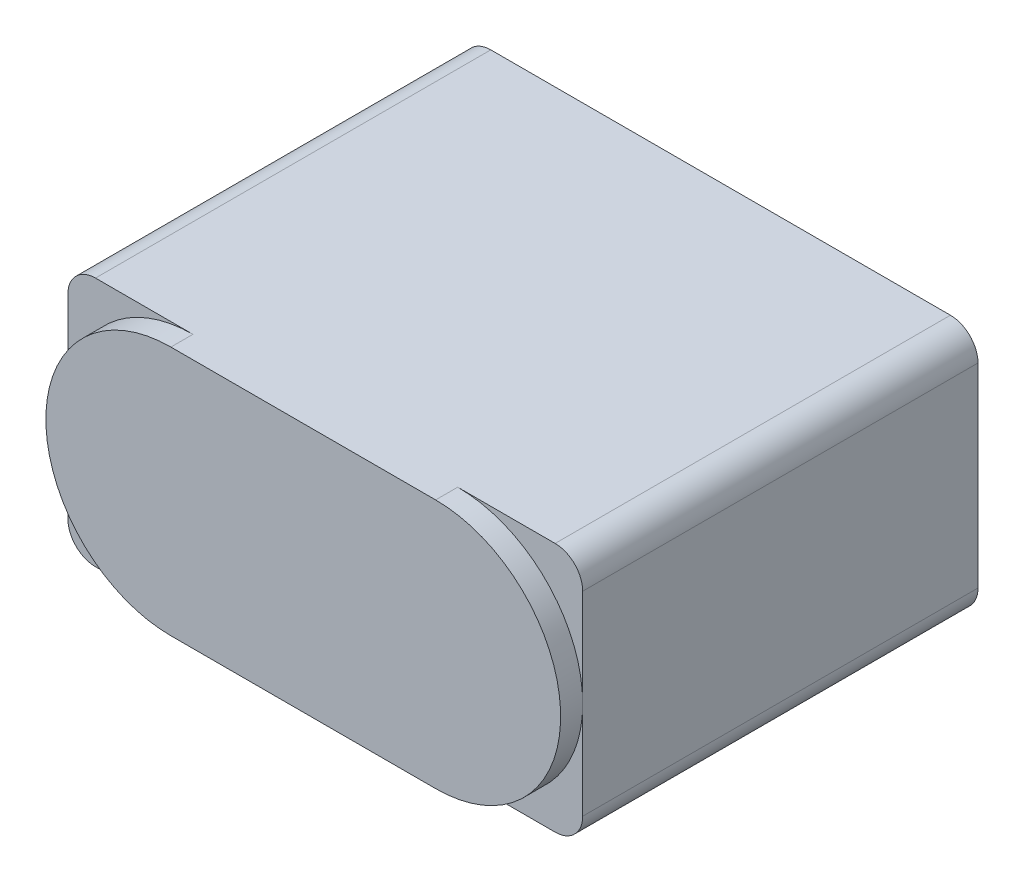
SolidWorks part; units mm, degrees
material "ABS"
ref_plane "前视基准面" through (0, 0, 0) normal (0, 0, 1) x (1, 0, 0)
ref_plane "上视基准面" through (0, 0, 0) normal (0, 1, 0) x (1, 0, 0)
ref_plane "右视基准面" through (0, 0, 0) normal (1, 0, 0) x (0, 0, -1)
sketch "草图1" plane through (0, 0, 0) normal (0, 0, 1) x (1, 0, 0)
  line L1 (1.5, 0) -> (26.5, 0)
  line L2 (0, 1.5) -> (0, 12.1)
  line L3 (1.5, 13.6) -> (26.5, 13.6)
  line L4 (28, 1.5) -> (28, 12.1)
  arc A0 (26.5, 0) -> (28, 1.5) centre (26.5, 1.5) ccw
  arc A1 (0, 12.1) -> (1.5, 13.6) centre (1.5, 12.1) cw
  arc A2 (26.5, 13.6) -> (28, 12.1) centre (26.5, 12.1) cw
  arc A3 (1.5, 0) -> (0, 1.5) centre (1.5, 1.5) cw
  point P7 (28, 0)
  point P10 (0, 13.6)
  point P15 (0, 0)
  dimension "D3" = 1.5
  dimension "D1" = 13.6
  dimension "D2" = 28
extrude "凸台-拉伸1" add sketch "草图1" along normal blind 22.7
sketch "草图2" plane through (0, 0, 22.7) normal (0, 0, 1) x (1, 0, 0)
  line L0 (6.8, 6.8) -> (21.2, 6.8) construction
  line L1 (6.8, 13.6) -> (21.2, 13.6)
  line L2 (6.8, 0) -> (21.2, 0)
  line L3 (14, 13.6) -> (14, -9.8871) construction
  line L4 (26.5, 13.6) -> (1.5, 13.6) construction
  line L5 (28, 6.8) -> (-1.3995, 6.8) construction
  line L6 (28, 1.5) -> (28, 12.1) construction
  line L7 (0, 12.1) -> (0, 1.5) construction
  line L12 (28, 1.5) -> (28, 12.1)
  line L13 (26.5, 13.6) -> (1.5, 13.6)
  line L14 (0, 12.1) -> (0, 1.5)
  line L15 (1.5, 0) -> (26.5, 0)
  line L16 (28, 1.5) -> (28, 12.1)
  line L17 (26.5, 13.6) -> (1.5, 13.6)
  line L18 (0, 12.1) -> (0, 1.5)
  line L19 (1.5, 0) -> (26.5, 0)
  arc A0 (6.8, 13.6) -> (6.8, 0) centre (6.8, 6.8) ccw
  arc A1 (21.2, 0) -> (21.2, 13.6) centre (21.2, 6.8) ccw
  arc A6 (26.5, 0) -> (28, 1.5) centre (26.5, 1.5) ccw
  arc A7 (28, 12.1) -> (26.5, 13.6) centre (26.5, 12.1) ccw
  arc A8 (1.5, 13.6) -> (0, 12.1) centre (1.5, 12.1) ccw
  arc A9 (0, 1.5) -> (1.5, 0) centre (1.5, 1.5) ccw
  arc A10 (26.5, 0) -> (28, 1.5) centre (26.5, 1.5) ccw
  arc A11 (28, 12.1) -> (26.5, 13.6) centre (26.5, 12.1) ccw
  arc A12 (1.5, 13.6) -> (0, 12.1) centre (1.5, 12.1) ccw
  arc A13 (0, 1.5) -> (1.5, 0) centre (1.5, 1.5) ccw
  point P2 (14, 6.8)
  arc M16 (26.5, 0) -> (28, 1.5) centre (26.5, 1.5) ccw
  line M17 (28, 1.5) -> (28, 12.1)
  arc M18 (28, 12.1) -> (26.5, 13.6) centre (26.5, 12.1) ccw
  line M19 (26.5, 13.6) -> (1.5, 13.6)
  arc M20 (1.5, 13.6) -> (0, 12.1) centre (1.5, 12.1) ccw
  line M21 (0, 12.1) -> (0, 1.5)
  arc M22 (0, 1.5) -> (1.5, 0) centre (1.5, 1.5) ccw
  line M23 (1.5, 0) -> (26.5, 0)
  dimension "D1" = 6.8
  dimension "D2" = 0
extrude "切除-拉伸1" cut sketch "草图2" against normal blind 1.2 contours A0 M19 M20 M21 | A0 L18 M22 M23 | A1 M23 M16 M17 | A1 L16 M18 M19
sketch "草图3" plane through (0, 0, 0) normal (0, 0, -1) x (-1, 0, 0)
  line L0 (-28, 6.8) -> (9.6728, 6.8) construction
  line L1 (-28, 1.5) -> (-28, 12.1) construction
  line L2 (-14, 13.6) -> (-14, -8.4705) construction
  line L3 (-26.5, 13.6) -> (-1.5, 13.6) construction
  line L5 (-18, 9.8) -> (-10, 9.8)
  line L6 (-18, 9.8) -> (-18, 3.8)
  line L7 (-18, 3.8) -> (-10, 3.8)
  line L8 (-10, 9.8) -> (-10, 3.8)
  circle A0 centre (-24.8, 6.8) radius 1.25
  circle A1 centre (-3.2, 6.8) radius 1.25
  dimension "D1" = 2.5
  dimension "D2" = 21.6
  dimension "D3" = 6
  dimension "D4" = 8
extrude "切除-拉伸2" cut sketch "草图3" against normal blind 5
cosmetic thread "装饰螺纹线3" parameters "D2"=3
cosmetic thread "装饰螺纹线4" parameters "D2"=3
sketch "草图4" plane through (0, 0, 0) normal (0, -1, 0) x (1, 0, 0)
  line L0 (6.8, 22.7) -> (21.2, 22.7) construction
  line L1 (14, 0) -> (14, 33.693) construction
  line L2 (1.5, 0) -> (26.5, 0) construction
  circle A0 centre (24.8, 11.6) radius 0.75
  circle A1 centre (3.2, 11.6) radius 0.75
  dimension "D3" = 1.5
  dimension "D1" = 11.1
  dimension "D2" = 21.6
extrude "切除-拉伸3" cut sketch "草图4" against normal blind 5
cosmetic thread "装饰螺纹线1" parameters "D2"=2
cosmetic thread "装饰螺纹线2" parameters "D2"=2
ref_plane "基准面1" through (0, 0, 262.7) normal (0, 0, 1) x (1, 0, 0)
sketch "草图5" plane through (0, 0, 262.7) normal (0, 0, 1) x (1, 0, 0)
  line L2 (21.2, 34.6) -> (6.8, 34.6)
  line L3 (6.8, -21) -> (21.2, -21)
  line L8 (6.8, 0) -> (21.2, 0)
  line L9 (21.2, 13.6) -> (6.8, 13.6)
  line L10 (6.8, 0) -> (21.2, 0) construction
  line L11 (21.2, 13.6) -> (6.8, 13.6) construction
  arc A2 (21.2, -21) -> (21.2, 34.6) centre (21.2, 6.8) ccw
  arc A3 (6.8, 34.6) -> (6.8, -21) centre (6.8, 6.8) ccw
  arc A8 (6.8, 13.6) -> (6.8, 0) centre (6.8, 6.8) ccw
  arc A9 (21.2, 0) -> (21.2, 13.6) centre (21.2, 6.8) ccw
  arc A10 (6.8, 13.6) -> (6.8, 0) centre (6.8, 6.8) ccw construction
  arc A11 (21.2, 0) -> (21.2, 13.6) centre (21.2, 6.8) ccw construction
  dimension "D3" = 0
  dimension "D1" = 21
sketch "草图6" plane through (0, 0, 22.7) normal (0, 0, 1) x (1, 0, 0)
  line L2 (6.8, 0) -> (21.2, 0)
  line L3 (21.2, 13.6) -> (6.8, 13.6)
  line L4 (6.8, 0) -> (21.2, 0)
  line L5 (21.2, 13.6) -> (6.8, 13.6)
  arc A2 (6.8, 13.6) -> (6.8, 0) centre (6.8, 6.8) ccw
  arc A3 (21.2, 0) -> (21.2, 13.6) centre (21.2, 6.8) ccw
  arc A4 (6.8, 13.6) -> (6.8, 0) centre (6.8, 6.8) ccw
  arc A5 (21.2, 0) -> (21.2, 13.6) centre (21.2, 6.8) ccw
  dimension "D1" = 0
loft "放样1" [suppressed] add profiles "草图6", "草图5"
